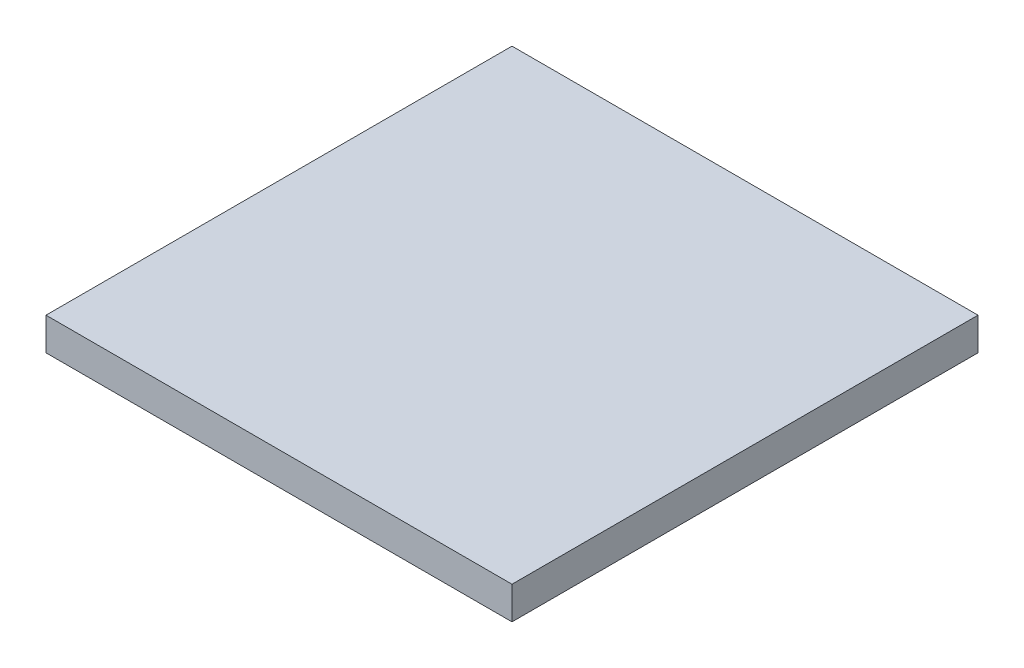
SolidWorks part; units mm, degrees
ref_plane "Front Plane" through (0, 0, 0) normal (0, 0, 1) x (1, 0, 0)
ref_plane "Top Plane" through (0, 0, 0) normal (0, 1, 0) x (1, 0, 0)
ref_plane "Right Plane" through (0, 0, 0) normal (1, 0, 0) x (0, 0, -1)
sketch "Sketch1" plane through (0, 0, 0) normal (1, 0, 0) x (0, 0, -1)
  line L1 (0, 0) -> (1000, 0)
  line L2 (0, 0) -> (0, 70)
  line L3 (0, 70) -> (1000, 70)
  line L4 (1000, 0) -> (1000, 70)
  dimension "D1" = 1000
  dimension "D2" = 70
extrude "Boss-Extrude1" add sketch "Sketch1" along normal blind 1000
